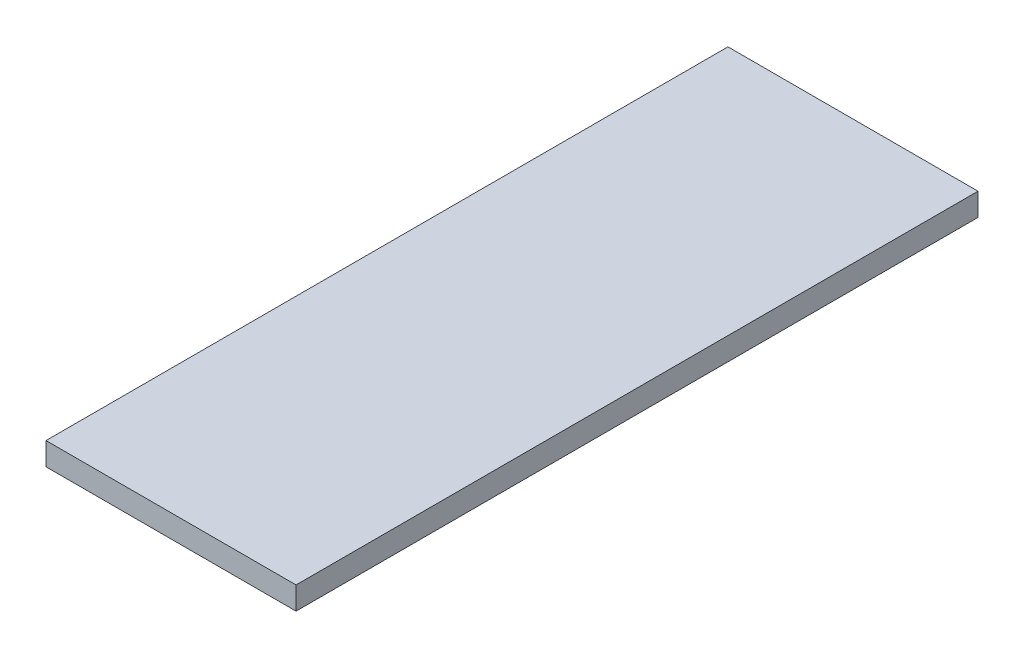
SolidWorks part; units mm, degrees
ref_plane "Front Plane" through (0, 0, 0) normal (0, 0, 1) x (1, 0, 0)
ref_plane "Top Plane" through (0, 0, 0) normal (0, 1, 0) x (1, 0, 0)
ref_plane "Right Plane" through (0, 0, 0) normal (1, 0, 0) x (0, 0, -1)
sketch "Sketch1" plane through (0, 0, 0) normal (0, 1, 0) x (1, 0, 0)
  line L0 (-55, -150) -> (55, -150)
  line L1 (-55, -150) -> (-55, 150)
  line L2 (-55, 150) -> (55, 150)
  line L3 (55, -150) -> (55, 150)
extrude "Boss-Extrude1" add sketch "Sketch1" along normal blind 10
